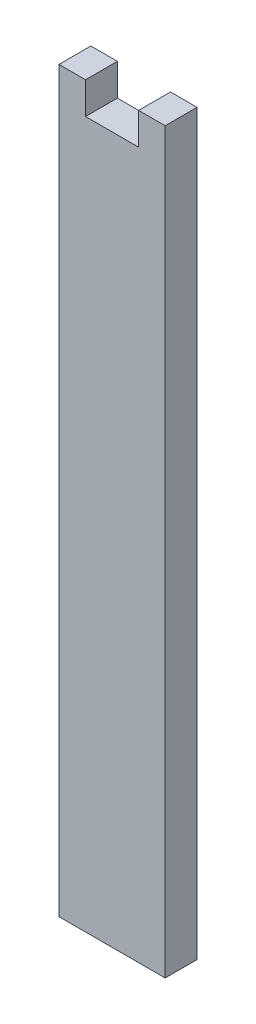
SolidWorks part; units mm, degrees
ref_plane "Front Plane" through (0, 0, 0) normal (0, 0, 1) x (1, 0, 0)
ref_plane "Top Plane" through (0, 0, 0) normal (0, 1, 0) x (1, 0, 0)
ref_plane "Right Plane" through (0, 0, 0) normal (1, 0, 0) x (0, 0, -1)
sketch "Sketch2" plane through (0, 0, 0) normal (0, 1, 0) x (1, 0, 0)
  line L0 (0, 0) -> (0, 6) construction
  dimension "D1" = 6
sketch "Sketch1" plane through (0, 0, 0) normal (0, 0, 1) x (1, 0, 0)
  line L0 (-5, 63.5) -> (0, 63.5)
  line L1 (-10, -69.5) -> (10, -69.5)
  line L2 (-10, -69.5) -> (-10, 69.5)
  line L3 (-10, 69.5) -> (10, 69.5)
  line L4 (10, -69.5) -> (10, 69.5)
  line L5 (-10, -69.5) -> (10, 69.5) construction
  line L6 (-10, 69.5) -> (10, -69.5) construction
  line L7 (10, 69.5) -> (5, 69.5)
  line L8 (10, 69.5) -> (10, 63.5)
  line L9 (10, 63.5) -> (5, 63.5)
  line L10 (5, 69.5) -> (5, 63.5)
  line L11 (-10, 69.5) -> (-5, 69.5)
  line L12 (-10, 69.5) -> (-10, 63.5)
  line L13 (-10, 63.5) -> (-5, 63.5)
  line L14 (-5, 69.5) -> (-5, 63.5)
  line L15 (0, 63.5) -> (5, 63.5)
  point P0 (0, 0)
  dimension "D1" = 20
  dimension "D2" = 139
  dimension "D3" = 6
extrude "Boss-Extrude1" add sketch "Sketch1" against normal up to vertex (6 mm away) contours L15 L0 L13 L2 L1 L4 L9 | L14 L3 L2 L13 | L3 L10 L9 L4 up to point (0, 0, -6)
equation "\"t_wood\"= 6' Thickness of the wood"
equation "\"t_glass\"= 2.5'Thickness of glass panels"
equation "\"w_glass\"= 248"
equation "\"h_glass\"= 167"
equation "\"h_food_internal\" = 60"
equation "\"entry_height\"= 20"
equation "\"entry diameter\"= 8"
equation "\"glass_bottom_overlap\"= 8"
equation "\"default_finger_size\"= 12"
equation "\"brood_depth\"= 42"
equation "\"outer_box_depth\" = \"brood_depth\" + ( 2 * \"t_glass\" ) + ( 2 * \"t_wood\" )"
equation "\"outer_box_width\"= \"w_glass\" + ( 2 * \"t_wood\" )"
equation "\"food_top_clearance\"= 10"
equation "\"outer_box_height\"= \"t_wood\" + \"h_glass\" + \"t_wood\" + \"h_food_internal\" + \"food_top_clearance\" + \"t_wood\""
equation "\"food_internal_depth\"= \"brood_depth\" + \"t_glass\" + \"t_glass\" - \"t_wood\" - \"t_wood\""
equation "\"food_channel_clearance_width\"= 14"
equation "\"bar_top_play\"= 4.5"
equation "\"bar_entry_angle\"= 10"
equation "\"bar_width\"= 20"
equation "\"entry_disk_play\"= 0.3"
equation "\"D1@Sketch2\"=\"t_wood\""
equation "\"D1@Sketch1\"=\"bar_width\""
equation "\"D2@Sketch1\"=\"h_glass\"-\"entry_height\"-\"entry diameter\""
equation "\"D3@Sketch1\"=\"t_wood\""
